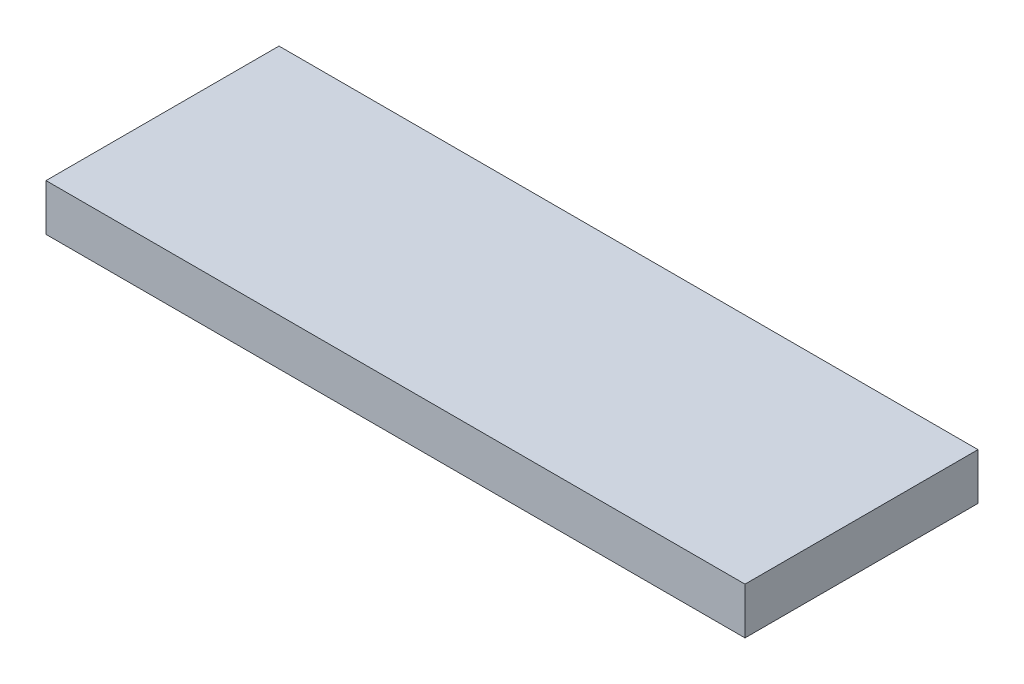
SolidWorks part; units mm, degrees
ref_plane "Front Plane" through (0, 0, 0) normal (0, 0, 1) x (1, 0, 0)
ref_plane "Top Plane" through (0, 0, 0) normal (0, 1, 0) x (1, 0, 0)
ref_plane "Right Plane" through (0, 0, 0) normal (1, 0, 0) x (0, 0, -1)
sketch "Sketch1" plane through (0, 0, 0) normal (0, 1, 0) x (1, 0, 0)
  line L1 (75, -25) -> (-75, -25)
  line L2 (75, -25) -> (75, 25)
  line L3 (75, 25) -> (-75, 25)
  line L4 (-75, -25) -> (-75, 25)
  line L5 (75, -25) -> (-75, 25) construction
  line L6 (75, 25) -> (-75, -25) construction
  point P0 (0, 0)
  dimension "D1" = 50
  dimension "D2" = 150
extrude "Boss-Extrude1" add sketch "Sketch1" along normal blind 10
